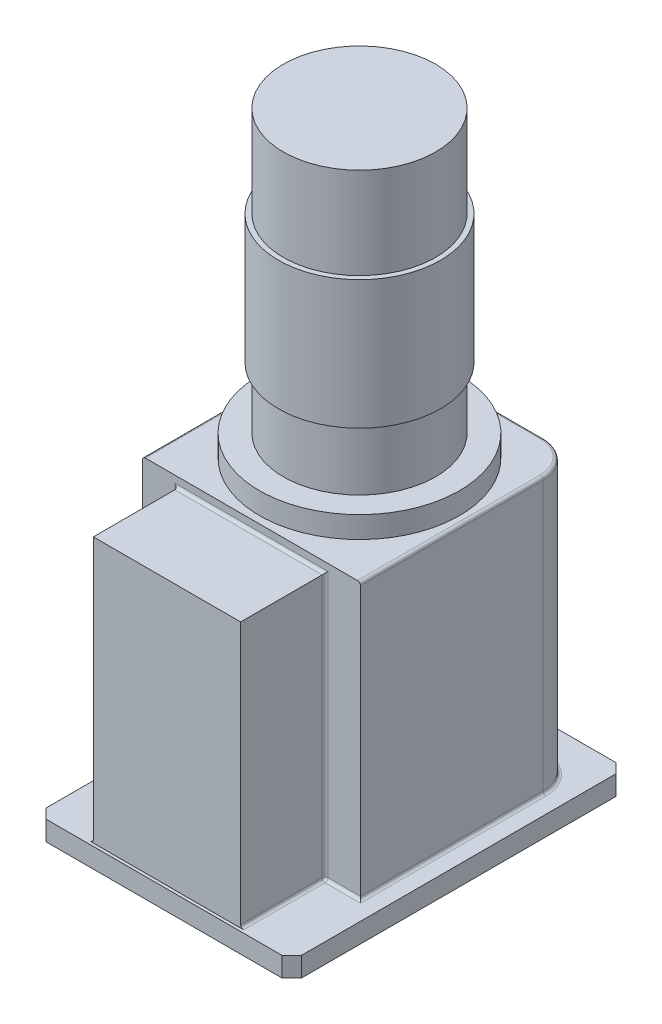
SolidWorks part; units mm, degrees
ref_plane "Alzado" through (0, 0, 0) normal (0, 0, 1) x (1, 0, 0)
ref_plane "Planta" through (0, 0, 0) normal (0, 1, 0) x (1, 0, 0)
ref_plane "Vista lateral" through (0, 0, 0) normal (1, 0, 0) x (0, 0, -1)
sketch "Croquis1" plane through (0, 0, 0) normal (0, 1, 0) x (1, 0, 0)
  line L1 (-130, -170) -> (130, -170)
  line L2 (-130, -170) -> (-130, 170)
  line L3 (-130, 170) -> (130, 170)
  line L4 (130, -170) -> (130, 170)
  line L5 (-130, -170) -> (130, 170) construction
  line L6 (-130, 170) -> (130, -170) construction
  point P0 (0, 0)
  dimension "D1" = 260
  dimension "D2" = 340
extrude "Saliente-Extruir1" add sketch "Croquis1" along normal blind 20
sketch "Croquis2" plane through (0, 20, 0) normal (0, 1, 0) x (1, 0, 0)
  line L0 (130, 170) -> (-130, 170) construction
  line L1 (-111, 140) -> (111, 140)
  line L2 (-111, 140) -> (-111, -81)
  line L3 (-111, -81) -> (111, -81)
  line L4 (111, 140) -> (111, -81)
  line L5 (-130, -170) -> (130, -170) construction
  line L6 (-130, 170) -> (-130, -170) construction
  line L7 (130, -170) -> (130, 170) construction
  dimension "D1" = 30
  dimension "D2" = 89
  dimension "D3" = 19
  dimension "D4" = 19
extrude "Saliente-Extruir2" add sketch "Croquis2" along normal blind 280
sketch "Croquis3" plane through (0, 20, 0) normal (0, 1, 0) x (1, 0, 0)
  line L0 (-75, -81) -> (75, -81)
  line L1 (-75, -81) -> (-75, -167)
  line L2 (75, -81) -> (75, -167)
  line L3 (-75, -167) -> (75, -167)
  line L4 (-111, -81) -> (111, -81) construction
  line L5 (-130, -170) -> (130, -170) construction
  line L6 (-130, 170) -> (-130, -170) construction
  dimension "D1" = 3
  dimension "D2" = 55
  dimension "D3" = 150
extrude "Saliente-Extruir3" add sketch "Croquis3" along normal blind 270
chamfer "Chaflán1" distance 10 angle 45 4 edges at (130, 10, 170) (-130, 10, 170) (-130, 10, -170) (130, 10, -170)
fillet "Redondeo1" radius 35 2 edges at (111, 160, -140) (-111, 160, -140)
fillet "Redondeo3" radius 3 17 edges at (111, 20, -12) (100.7487, 20, -129.7487) (0, 20, -140) (-100.7487, 20, -129.7487) (111, 300, -12) (100.7487, 300, -129.7487) (0, 300, -140) (-100.7487, 300, -129.7487) (0, 290, 81) (93, 20, 81) (75, 155, 81) (75, 20, 124) (-75, 20, 124) (-93, 20, 81) (-111, 20, -12) (-111, 300, -12) (-75, 155, 81)
ref_plane "Plano1" through (0.86, 0, 0) normal (-1, 0, 0) x (0, 0, 1)
sketch "Croquis4" plane through (0.86, 0, 0) normal (-1, 0, 0) x (0, 0, 1)
  line L0 (-28.14, 300) -> (-28.14, 743.7376) construction
  line L2 (-105, 300) -> (81, 300) construction
  line L3 (-140, 23) -> (-140, 297) construction
  line L4 (-28.14, 300) -> (-130, 300)
  line L5 (-130, 300) -> (-130, 322)
  line L6 (-130, 322) -> (-105.64, 322)
  line L7 (-105.64, 322) -> (-105.64, 384.5)
  line L8 (-105.64, 384.5) -> (-110.64, 384.5)
  line L9 (-110.64, 384.5) -> (-110.64, 515.5)
  line L10 (-110.64, 515.5) -> (-105.64, 515.5)
  line L11 (-105.64, 515.5) -> (-105.64, 608.5)
  line L12 (-105.64, 608.5) -> (-28.14, 608.5)
  line L13 (-28.14, 300) -> (-28.14, 608.5)
  dimension "D1" = 111.86
  dimension "D2" = 22
  dimension "D3" = 62.5
  dimension "D4" = 131
  dimension "D5" = 93
  dimension "D6" = 203.72
  dimension "D7" = 155
  dimension "D8" = 165
revolve "Revolución1" add sketch "Croquis4" angle 360 about L0
